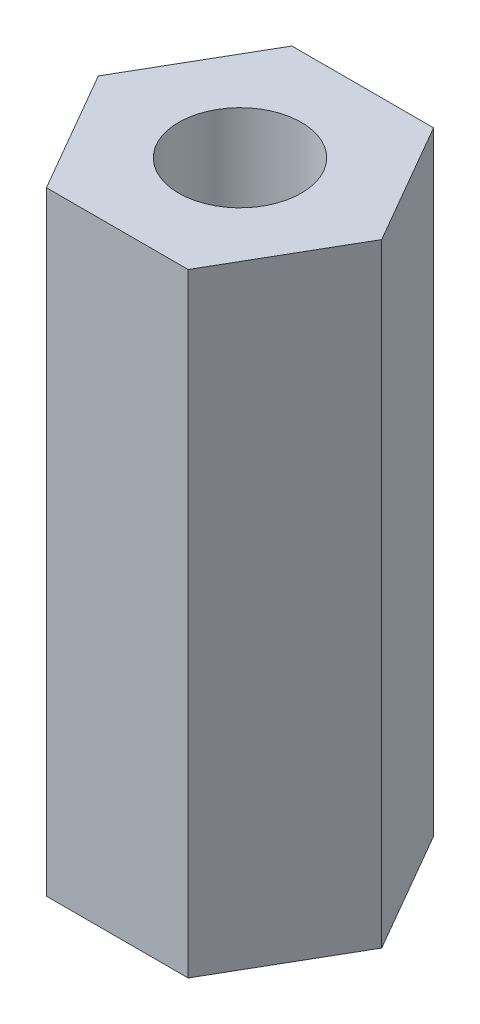
SolidWorks part; units mm, degrees
ref_plane "Front Plane" through (0, 0, 0) normal (0, 0, 1) x (1, 0, 0)
ref_plane "Top Plane" through (0, 0, 0) normal (0, 1, 0) x (1, 0, 0)
ref_plane "Right Plane" through (0, 0, 0) normal (1, 0, 0) x (0, 0, -1)
sketch "Sketch1" plane through (0, 0, 0) normal (0, 1, 0) x (1, 0, 0)
  line L1 (3.4641, 0) -> (1.7321, 3)
  line L2 (1.7321, 3) -> (-1.7321, 3)
  line L3 (-1.7321, 3) -> (-3.4641, 0)
  line L4 (-3.4641, 0) -> (-1.7321, -3)
  line L5 (-1.7321, -3) -> (1.7321, -3)
  line L6 (1.7321, -3) -> (3.4641, 0)
  circle A0 centre (0, 0) radius 3 construction
  circle A1 centre (0, 0) radius 1.5
  dimension "D1" = 3
  dimension "D2" = 6
extrude "Boss-Extrude1" add sketch "Sketch1" along normal blind 15
